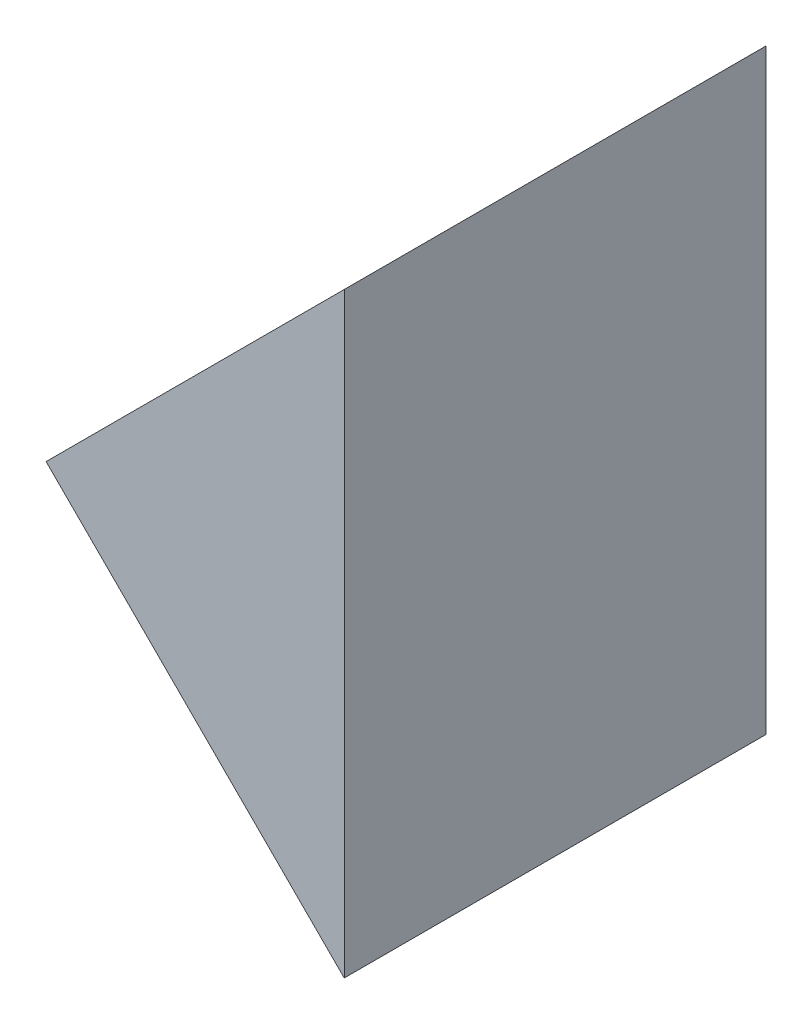
SolidWorks part; units mm, degrees
ref_plane "前视基准面" through (0, 0, 0) normal (0, 0, 1) x (1, 0, 0)
ref_plane "上视基准面" through (0, 0, 0) normal (0, 1, 0) x (1, 0, 0)
ref_plane "右视基准面" through (0, 0, 0) normal (1, 0, 0) x (0, 0, -1)
sketch "草图1" plane through (0, 0, 0) normal (0, 0, 1) x (1, 0, 0)
  line L0 (554.7667, 137.7569) -> (590.122, 173.1123)
  line L1 (554.7667, 137.7569) -> (590.122, 102.4016)
  line L2 (590.122, 102.4016) -> (590.122, 173.1123)
  dimension "D1" = 50
extrude "凸台-拉伸1" add sketch "草图1" along normal blind 50
